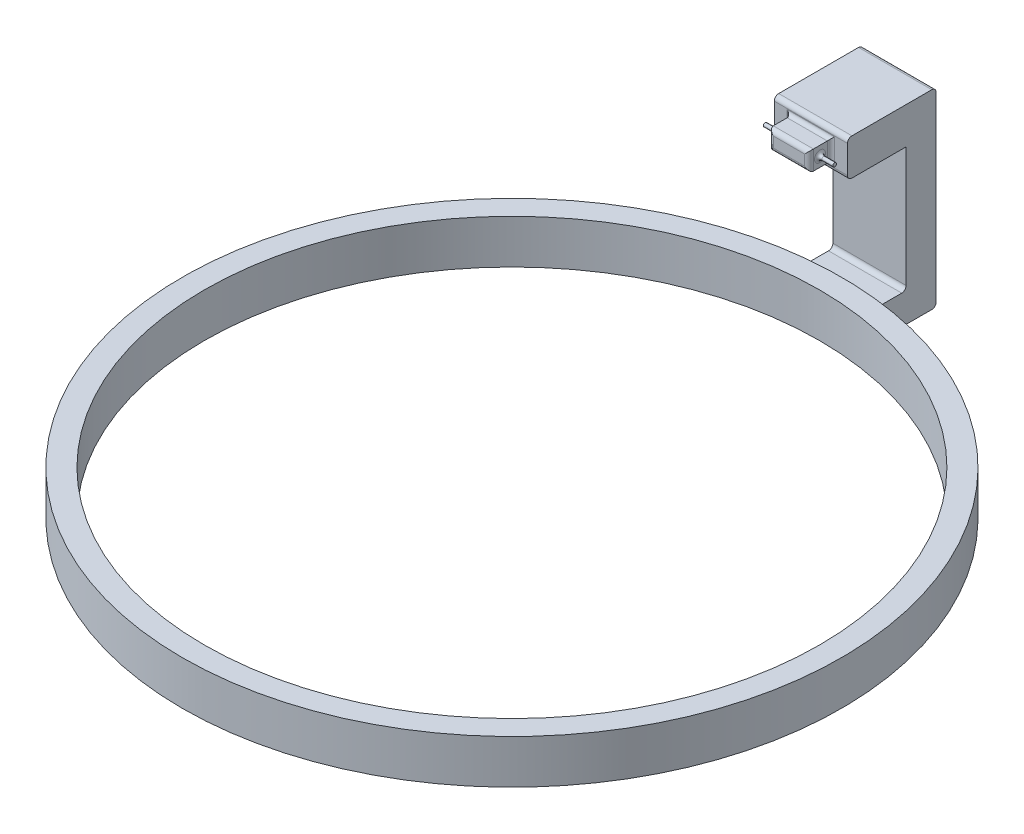
SolidWorks part; units mm, degrees
ref_plane "Front Plane" through (0, 0, 0) normal (0, 0, 1) x (1, 0, 0)
ref_plane "Top Plane" through (0, 0, 0) normal (0, 1, 0) x (1, 0, 0)
ref_plane "Right Plane" through (0, 0, 0) normal (1, 0, 0) x (0, 0, -1)
sketch "Sketch1" plane through (0, 0, 0) normal (0, 1, 0) x (1, 0, 0)
  circle A0 centre (0, 0) radius 225
  dimension "D1" = 450
extrude "Boss-Extrude1" add sketch "Sketch1" along normal blind 30
sketch "Sketch2" plane through (0, 30, 0) normal (0, 1, 0) x (1, 0, 0)
  circle A0 centre (0, 0) radius 210
  dimension "D1" = 420
extrude "Cut-Extrude1" cut sketch "Sketch2" against normal through all both and the other way through all
ref_plane "Plane1" through (0, 0, -214.6194) normal (0, 0, 1) x (1, 0, 0)
sketch "Sketch3" plane through (0, 0, -214.6194) normal (0, 0, 1) x (1, 0, 0)
  line L1 (25, 25) -> (-25, 25)
  line L2 (25, 25) -> (25, 5)
  line L3 (25, 5) -> (-25, 5)
  line L4 (-25, 25) -> (-25, 5)
  dimension "D1" = 50
  dimension "D2" = 20
extrude "Boss-Extrude2" add sketch "Sketch3" against normal blind 50
sketch "Sketch4" plane through (0, 25, 0) normal (0, 1, 0) x (1, 0, 0)
  line L0 (-25, 264.6194) -> (-25, 223.6068) construction
  line L1 (25, 264.6194) -> (-25, 264.6194)
  line L2 (25, 264.6194) -> (25, 244.1131)
  line L3 (25, 244.1131) -> (-25, 244.1131)
  line L4 (-25, 264.6194) -> (-25, 244.1131)
extrude "Boss-Extrude3" add sketch "Sketch4" along normal blind 110
sketch "Sketch5" plane through (0, 0, -244.1131) normal (0, 0, 1) x (1, 0, 0)
  line L0 (-25, 135) -> (-25, 25) construction
  line L1 (-25, 135) -> (25, 135)
  line L2 (-25, 135) -> (-25, 110)
  line L3 (-25, 110) -> (25, 110)
  line L4 (25, 135) -> (25, 110)
  line L7 (-25, 135) -> (25, 135) construction
  dimension "D1" = 50
  dimension "D2" = 25
extrude "Boss-Extrude7" add sketch "Sketch5" along normal blind 40
sketch "Sketch6" plane through (0, 0, -204.1131) normal (0, 0, 1) x (1, 0, 0)
  line L0 (0, 135) -> (0, 80) construction
  line L1 (-13.6962, 115.935) -> (13.6962, 115.935)
  line L2 (-13.6962, 115.935) -> (-13.6962, 129.065)
  line L3 (-13.6962, 129.065) -> (13.6962, 129.065)
  line L4 (13.6962, 115.935) -> (13.6962, 129.065)
  line L5 (25, 135) -> (-25, 135) construction
  line L7 (25, 110) -> (25, 135) construction
  line L8 (-25, 122.5) -> (25, 122.5) construction
  line L9 (-25, 135) -> (-25, 110) construction
  dimension "D1" = 27.3924
  dimension "D2" = 13.13
extrude "Boss-Extrude8" add sketch "Sketch6" along normal blind 15
sketch "Sketch7" plane through (-13.6962, 0, 0) normal (-1, 0, 0) x (0, 0, 1)
  line L0 (-196.6131, 115.935) -> (-196.6131, 129.065) construction
  line L1 (-189.1131, 115.935) -> (-204.1131, 115.935) construction
  line L2 (-189.1131, 129.065) -> (-204.1131, 129.065) construction
  line L3 (-204.1131, 122.5) -> (-189.1131, 122.5) construction
  line L4 (-204.1131, 115.935) -> (-204.1131, 129.065) construction
  line L5 (-189.1131, 115.935) -> (-189.1131, 129.065) construction
  circle A0 centre (-196.6131, 122.5) radius 1.25
  point P15 (-196.6131, 122.5)
  dimension "D1" = 2.5
extrude "Boss-Extrude9" add sketch "Sketch7" along normal blind 10
sketch "Sketch8" plane through (13.6962, 0, 0) normal (1, 0, 0) x (0, 0, -1)
  line L0 (196.6131, 115.935) -> (196.6131, 129.065) construction
  line L1 (189.1131, 115.935) -> (204.1131, 115.935) construction
  line L2 (189.1131, 129.065) -> (204.1131, 129.065) construction
  line L3 (189.1131, 122.5) -> (204.1131, 122.5) construction
  line L4 (189.1131, 129.065) -> (189.1131, 115.935) construction
  line L5 (204.1131, 129.065) -> (204.1131, 115.935) construction
  circle A0 centre (196.6131, 122.5) radius 1.25
  dimension "D1" = 2.5
extrude "Boss-Extrude10" add sketch "Sketch8" along normal blind 10
fillet "Fillet14" radius 3 4 edges at (13.6962, 122.5, -189.1131) (0, 115.935, -189.1131) (-13.6962, 122.5, -189.1131) (0, 129.065, -189.1131)
fillet "Fillet15" radius 2.5 6 edges at (0, 115.935, -204.1131) (13.6962, 122.5, -204.1131) (-13.6962, 122.5, -204.1131) (0, 129.065, -204.1131) (-13.6962, 123.75, -196.6131) (13.6962, 122.5, -195.3631)
fillet "Fillet17" radius 3 9 edges at (25, 15, -223.6068) (0, 5, -225) (-25, 15, -223.6068) (0, 25, -225) (0, 5, -264.6194) (0, 25, -244.1131) (0, 135, -264.6194) (0, 110, -204.1131) (0, 135, -204.1131)
